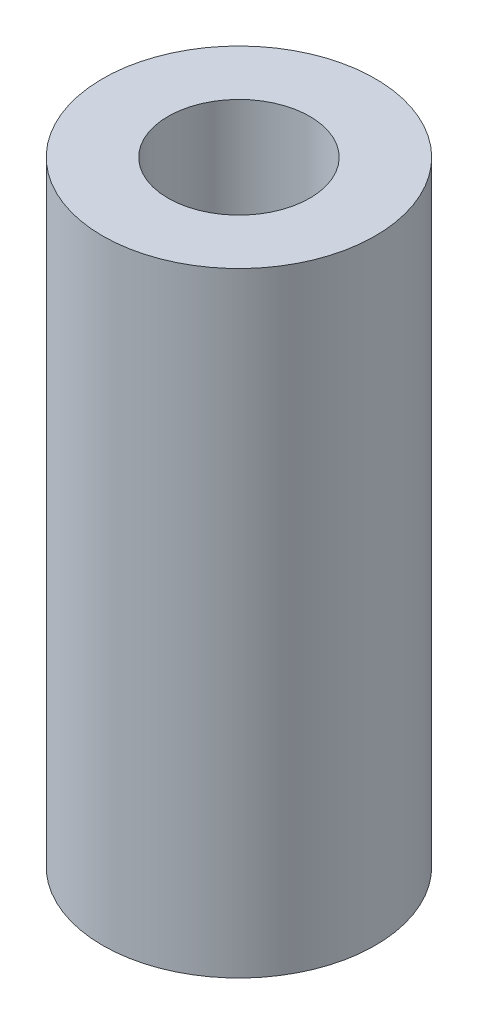
SolidWorks part; units mm, degrees
ref_plane "Front Plane" through (0, 0, 0) normal (0, 0, 1) x (1, 0, 0)
ref_plane "Top Plane" through (0, 0, 0) normal (0, 1, 0) x (1, 0, 0)
ref_plane "Right Plane" through (0, 0, 0) normal (1, 0, 0) x (0, 0, -1)
sketch "Sketch2" plane through (0, 0, 0) normal (0, 1, 0) x (1, 0, 0)
  circle A0 centre (0, 0) radius 1.905
  circle A1 centre (0, 0) radius 3.6622
  dimension "D1" = 3.81
extrude "Boss-Extrude1" add sketch "Sketch2" along normal blind 16.51
